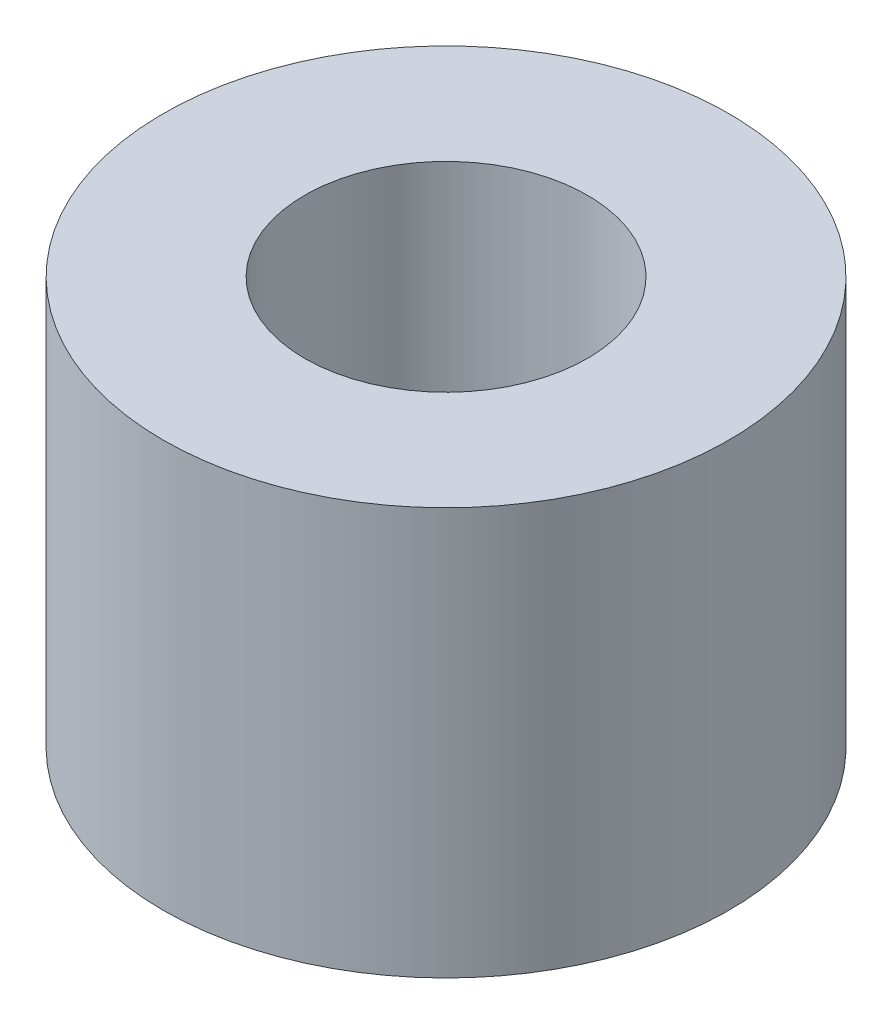
SolidWorks part; units mm, degrees
ref_plane "Front Plane" through (0, 0, 0) normal (0, 0, 1) x (1, 0, 0)
ref_plane "Top Plane" through (0, 0, 0) normal (0, 1, 0) x (1, 0, 0)
ref_plane "Right Plane" through (0, 0, 0) normal (1, 0, 0) x (0, 0, -1)
sketch "Sketch1" plane through (0, 0, 0) normal (0, 1, 0) x (1, 0, 0)
  circle A0 centre (0, 0) radius 23
  circle A1 centre (0, 0) radius 11.5
  dimension "D1" = 46
  dimension "D2" = 23
extrude "Boss-Extrude1" add sketch "Sketch1" along normal blind 33.12
